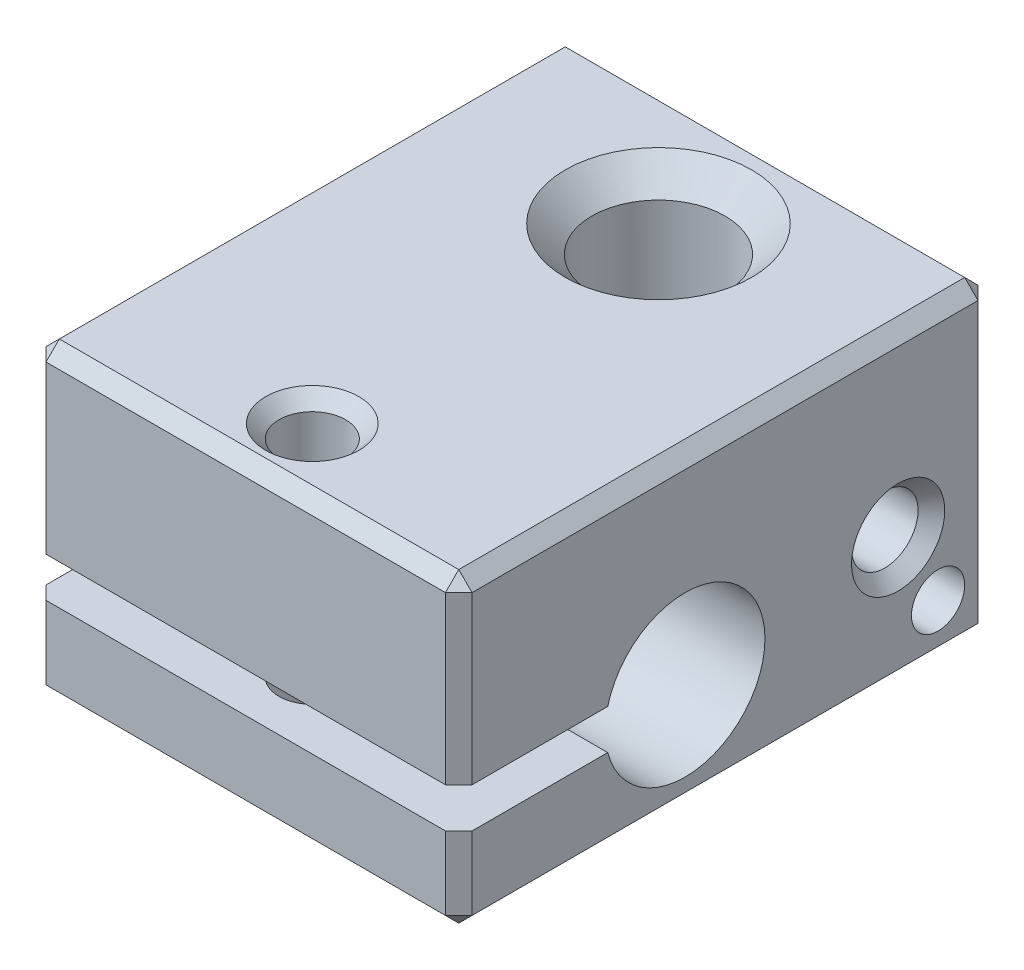
SolidWorks part; units mm, degrees
ref_plane "Спереди" through (0, 0, 0) normal (0, 0, 1) x (1, 0, 0)
ref_plane "Сверху" through (0, 0, 0) normal (0, 1, 0) x (1, 0, 0)
ref_plane "Справа" through (0, 0, 0) normal (1, 0, 0) x (0, 0, -1)
sketch "Эскиз1" plane through (0, 0, 0) normal (1, 0, 0) x (0, 0, -1)
  line L1 (10, -5.75) -> (-10, -5.75)
  line L2 (10, -5.75) -> (10, 5.75)
  line L3 (10, 5.75) -> (-10, 5.75)
  line L4 (-10, -5.75) -> (-10, 5.75)
  line L5 (10, -5.75) -> (-10, 5.75) construction
  line L6 (10, 5.75) -> (-10, -5.75) construction
  point P0 (0, 0)
  dimension "D1" = 11.5
  dimension "D2" = 20
extrude "Бобышка-Вытянуть1" add sketch "Эскиз1" along normal mid plane 16
sketch "Эскиз2" plane through (8, 0, 0) normal (1, 0, 0) x (0, 0, -1)
  line L0 (10, -5.75) -> (10, 5.75) construction
  line L1 (-10, -5.75) -> (10, -5.75) construction
  line L2 (-1.5, -1.75) -> (-10, -1.75) construction
  line L3 (-10, 5.75) -> (-10, -5.75) construction
  line L4 (-10, -1) -> (-4.4047, -1)
  line L5 (-10, -2.5) -> (-4.4047, -2.5)
  line L6 (-10, -1) -> (-10, -2.5)
  arc A0 (-4.4047, -2.5) -> (-4.4047, -1) centre (-1.5, -1.75) ccw
  dimension "D1" = 6
  dimension "D2" = 11.5
  dimension "D3" = 4
  dimension "D4" = 1.5
extrude "Вырез-Вытянуть1" cut sketch "Эскиз2" against normal up to next
hole_wizard "Отверстие обработанное метчиком M31" positions "Эскиз4" profile "Эскиз3" tap size "M3" standard "ISO"
sketch "Эскиз4" plane through (0, 5.75, 0) normal (0, 1, 0) x (-1, 0, 0)
  line L1 (0, 0) -> (0, 7.5) construction
  line L3 (-8, -10) -> (-8, 10) construction
  line L4 (-8, -10) -> (8, -10) construction
  point P0 (0, 7.5)
  dimension "D1" = 8
  dimension "D2" = 17.5
sketch "Эскиз3" plane through (0, 5.75, 7.5) normal (1, 0, 0) x (0, 0, 1)
  line L0 (0, 0) -> (0, 12.2511)
  line L1 (0, 12.2511) -> (1.25, 11.5)
  line L2 (1.25, 11.5) -> (1.25, 0)
  line L5 (1.25, 0) -> (0, 0)
  line L10 (0, 12.2511) -> (-1.25, 11.5) construction
  line L11 (0, -6.35) -> (0, 107.95) construction
  dimension "Диаметр сверла" = 2.5
  dimension "Глубина сверла" = 11.5
  dimension "Угол заточки сверла" = 118
cosmetic thread "Отверстие резьбы1" parameters "D1"=11.5, "D2"=3
hole_wizard "Отверстие обработанное метчиком M61" positions "Эскиз6" profile "Эскиз7" tap size "M6" standard "ISO" end condition up to next
sketch "Эскиз6" plane through (0, 5.75, 0) normal (0, 1, 0) x (-1, 0, 0)
  line L0 (0, -5.5) -> (0, 0) construction
  line L2 (-8, -10) -> (8, -10) construction
  point P0 (0, -5.5)
  dimension "D1" = 4.5
sketch "Эскиз7" plane through (0, 5.75, -5.5) normal (1, 0, 0) x (0, 0, 1)
  line L0 (0, 0) -> (0, 11.5)
  line L1 (0, 11.5) -> (2.5, 11.5)
  line L2 (2.5, 11.5) -> (2.5, 0)
  line L5 (2.5, 0) -> (0, 0)
  line L11 (0, -6.35) -> (0, 107.95) construction
  dimension "Диаметр проходного сверла" = 5
  dimension "Глубина проходного сверла" = 11.5
cosmetic thread "Отверстие резьбы2" parameters "D2"=6
chamfer "Фаска1" distance 0.5 angle 45 2 edges at (0, -5.75, 8.75) (0, 5.75, 8.75)
chamfer "Фаска2" distance 1 angle 45 2 edges at (0, -5.75, -3) (0, 5.75, -3)
hole_wizard "Отверстие обработанное метчиком M32" positions "Эскиз9" profile "Эскиз8" tap size "M3" standard "ISO"
sketch "Эскиз9" plane through (8, 0, 0) normal (1, 0, 0) x (0, 0, -1)
  line L0 (-10, -5.75) -> (10, -5.75) construction
  line L1 (10, -5.75) -> (10, 5.75) construction
  point P0 (6.5, -0.95)
  dimension "D1" = 4.8
  dimension "D2" = 3.5
sketch "Эскиз8" plane through (8, -0.95, -6.5) normal (0, 1, 0) x (0, 0, -1)
  line L0 (0, 0) -> (0, 4.5511)
  line L1 (0, 4.5511) -> (1.25, 3.8)
  line L2 (1.25, 3.8) -> (1.25, 0)
  line L5 (1.25, 0) -> (0, 0)
  line L10 (0, 4.5511) -> (-1.25, 3.8) construction
  line L11 (0, -6.35) -> (0, 107.95) construction
  dimension "Диаметр сверла" = 2.5
  dimension "Глубина сверла" = 3.8
  dimension "Угол заточки сверла" = 118
cosmetic thread "Отверстие резьбы3" parameters "D1"=3.4, "D2"=3
chamfer "Фаска3" distance 0.5 angle 45 1 edges at (8, -0.95, -7.75)
hole_wizard "Отверстие1" positions "Эскиз11" profile "Эскиз10" legacy
sketch "Эскиз11" plane through (8, 0, 0) normal (1, 0, 0) x (0, 0, -1)
  line L0 (10, -5.75) -> (10, 5.75) construction
  line L1 (-10, -5.75) -> (10, -5.75) construction
  point P0 (8, -3.75)
  dimension "D1" = 2
  dimension "D2" = 2
sketch "Эскиз10" plane through (8, -3.75, -8) normal (0, 1, 0) x (0, 0, -1)
  line L0 (0, 0) -> (0, 4.8506)
  line L1 (0, 4.8506) -> (0.75, 4.4)
  line L2 (0.75, 4.4) -> (0.75, 0)
  line L4 (0.75, 0) -> (0, 0)
  line L6 (0, 4.8506) -> (-0.75, 4.4) construction
  line L7 (0, -4.2442) -> (0, 117.3081) construction
  dimension "Диаметр" = 1.5
  dimension "Глубина" = 4.4
  dimension "Угол заточки сверла" = 118
hole_wizard "Отверстие2" positions "Эскиз13" profile "Эскиз12" legacy
sketch "Эскиз13" plane through (8, 0, 0) normal (1, 0, 0) x (0, 0, -1)
  point P0 (8, -3.75)
sketch "Эскиз12" plane through (8, -3.75, -8) normal (0, 1, 0) x (0, 0, -1)
  line L0 (0, 0) -> (0, 2.6009)
  line L1 (0, 2.6009) -> (1, 2)
  line L2 (1, 2) -> (1, 0)
  line L4 (1, 0) -> (0, 0)
  line L6 (0, 2.6009) -> (-1, 2) construction
  line L7 (0, -4.2442) -> (0, 117.3081) construction
  dimension "Диаметр" = 2
  dimension "Глубина" = 2
  dimension "Угол заточки сверла" = 118
chamfer "Фаска4" distance 0.5 angle 45 14 edges at (-8, -5.75, 0) (-8, -4.125, 10) (0, -5.75, 10) (8, -4.125, 10) (8, -5.75, 0) (0, -5.75, -10) (8, 0, -10) (-8, 0, -10) (0, 5.75, -10) (-8, 5.75, 0) (-8, 2.375, 10) (0, 5.75, 10) (8, 5.75, 0) (8, 2.375, 10)
